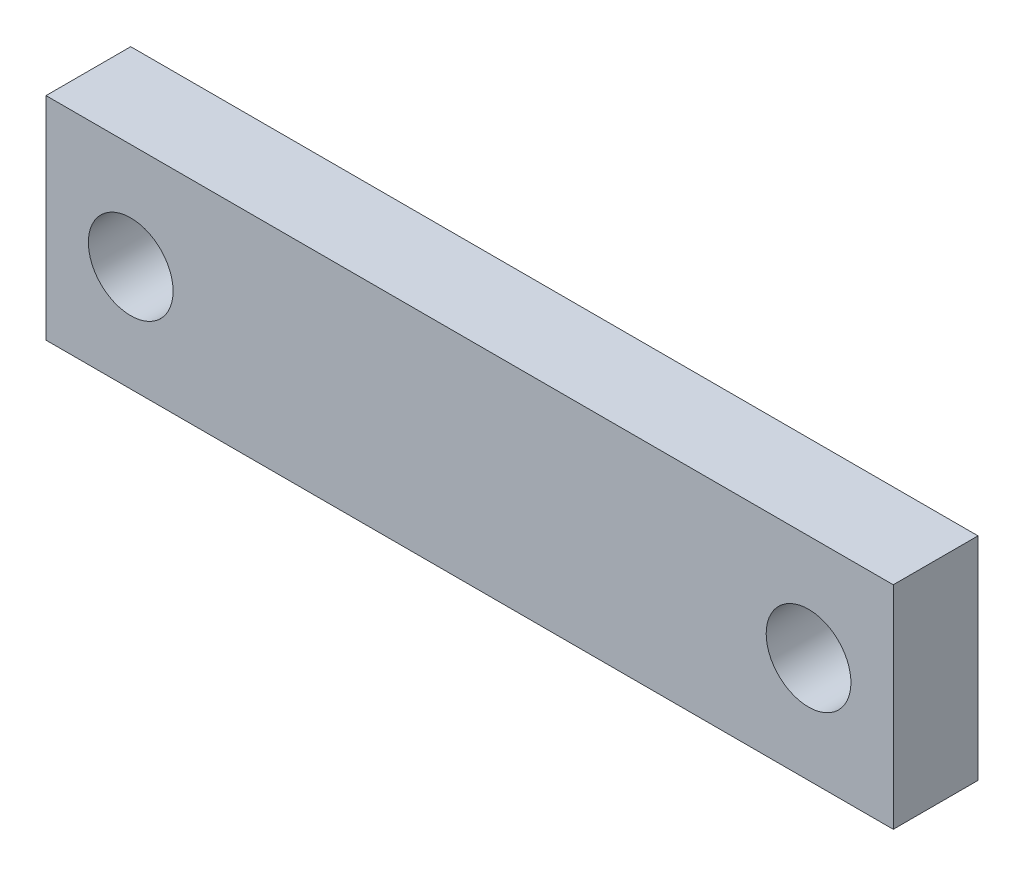
SolidWorks part; units mm, degrees
ref_plane "Front Plane" through (0, 0, 0) normal (0, 0, 1) x (1, 0, 0)
ref_plane "Top Plane" through (0, 0, 0) normal (0, 1, 0) x (1, 0, 0)
ref_plane "Right Plane" through (0, 0, 0) normal (1, 0, 0) x (0, 0, -1)
sketch "Sketch1" plane through (0, 0, 0) normal (0, 0, 1) x (1, 0, 0)
  line L0 (0, 2.5) -> (0, -2.5) construction
  line L1 (-10, 2.5) -> (10, 2.5)
  line L2 (-10, 2.5) -> (-10, -2.5)
  line L3 (-10, -2.5) -> (10, -2.5)
  line L4 (10, 2.5) -> (10, -2.5)
  line L5 (-10, 2.5) -> (10, -2.5) construction
  line L6 (-10, -2.5) -> (10, 2.5) construction
  circle A0 centre (-8, 0) radius 1
  circle A1 centre (8, 0) radius 1
  point P0 (0, 0)
  dimension "D3" = 2
  dimension "D4" = 2
  dimension "D1" = 20
  dimension "D2" = 5
extrude "Boss-Extrude1" add sketch "Sketch1" along normal blind 2
